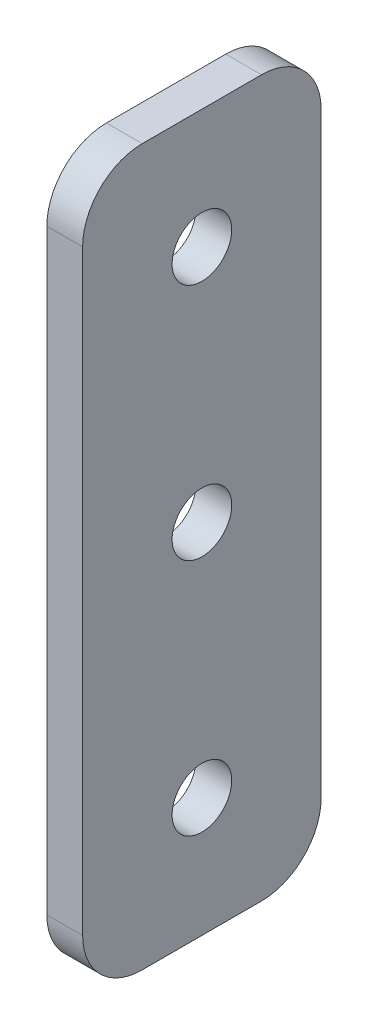
SolidWorks part; units mm, degrees
ref_plane "Front Plane" through (0, 0, 0) normal (0, 0, 1) x (1, 0, 0)
ref_plane "Top Plane" through (0, 0, 0) normal (0, 1, 0) x (1, 0, 0)
ref_plane "Right Plane" through (0, 0, 0) normal (1, 0, 0) x (0, 0, -1)
sketch "Sketch1" plane through (0, 0, 0) normal (1, 0, 0) x (0, 0, -1)
  line L1 (-10, 60) -> (10, 60)
  line L2 (-10, 60) -> (-10, 0)
  line L3 (-10, 0) -> (10, 0)
  line L4 (10, 60) -> (10, 0)
  circle A0 centre (0, 10) radius 2.5
  circle A1 centre (0, 30) radius 2.5
  circle A2 centre (0, 50) radius 2.5
  point P4 (0, 0)
  dimension "D3" = 5
  dimension "D4" = 10
  dimension "D5" = 20
  dimension "D6" = 20
  dimension "D1" = 20
  dimension "D2" = 60
extrude "Boss-Extrude1" add sketch "Sketch1" along normal blind 3
fillet "Fillet1" radius 5 4 edges at (1.5, 0, -10) (1.5, 0, 10) (1.5, 60, -10) (1.5, 60, 10)
